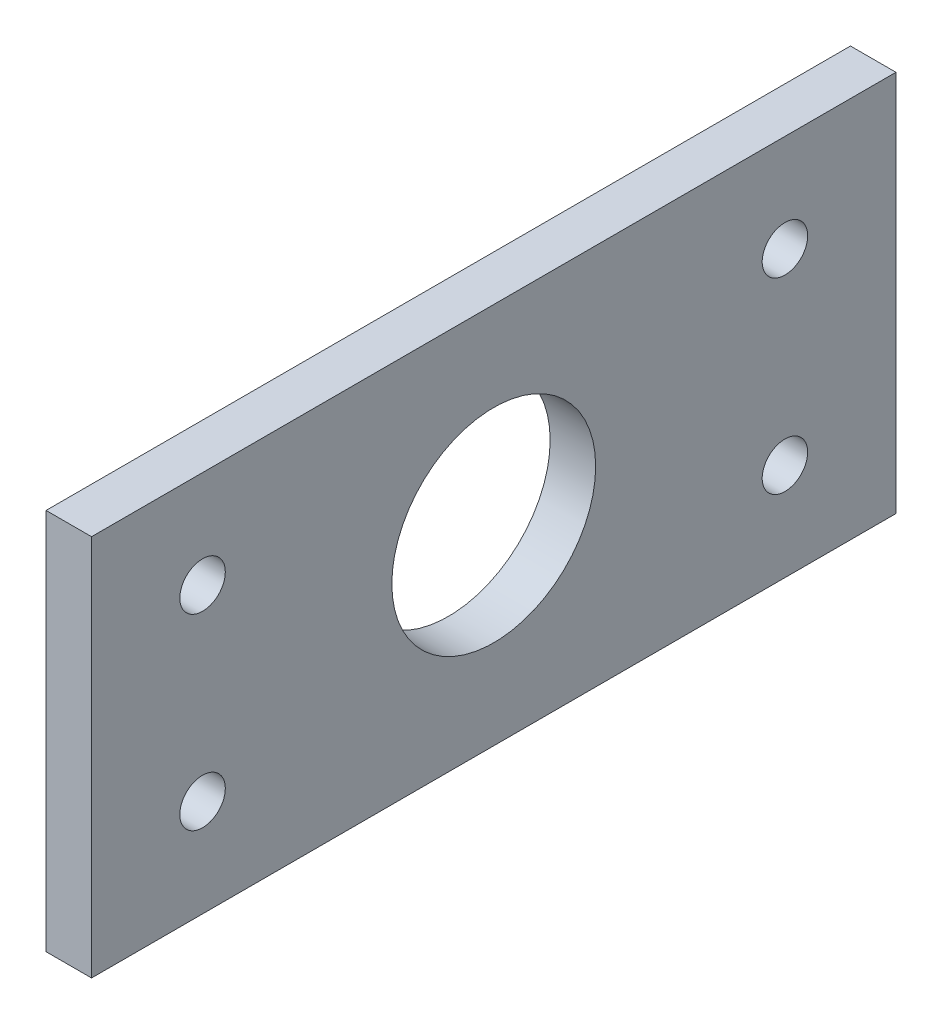
SolidWorks part; units mm, degrees
material "1060 Alloy"
ref_plane "Front Plane" through (0, 0, 0) normal (0, 0, 1) x (1, 0, 0)
ref_plane "Top Plane" through (0, 0, 0) normal (0, 1, 0) x (1, 0, 0)
ref_plane "Right Plane" through (0, 0, 0) normal (1, 0, 0) x (0, 0, -1)
sketch "Sketch1" plane through (0, 0, 0) normal (1, 0, 0) x (0, 0, -1)
  line L1 (-56.134, -26.67) -> (56.134, -26.67)
  line L2 (-56.134, -26.67) -> (-56.134, 26.67)
  line L3 (-56.134, 26.67) -> (56.134, 26.67)
  line L4 (56.134, -26.67) -> (56.134, 26.67)
  line L5 (-56.134, -26.67) -> (56.134, 26.67) construction
  line L6 (-56.134, 26.67) -> (56.134, -26.67) construction
  circle A0 centre (0, 0) radius 14.224
  circle A1 centre (-40.64, -13.081) radius 3.175
  circle A2 centre (40.64, -13.081) radius 3.175
  circle A3 centre (-40.64, 13.081) radius 3.175
  circle A4 centre (40.64, 13.081) radius 3.175
  point P0 (0, 0)
  dimension "D3" = 28.448
  dimension "D4" = 6.35
  dimension "D5" = 6.35
  dimension "D6" = 13.589
  dimension "D7" = 15.494
  dimension "D8" = 13.589
  dimension "D9" = 15.494
  dimension "D10" = 13.589
  dimension "D11" = 13.589
  dimension "D12" = 15.494
  dimension "D13" = 15.494
  dimension "D1" = 112.268
  dimension "D2" = 53.34
extrude "Boss-Extrude1" add sketch "Sketch1" along normal blind 6.35
